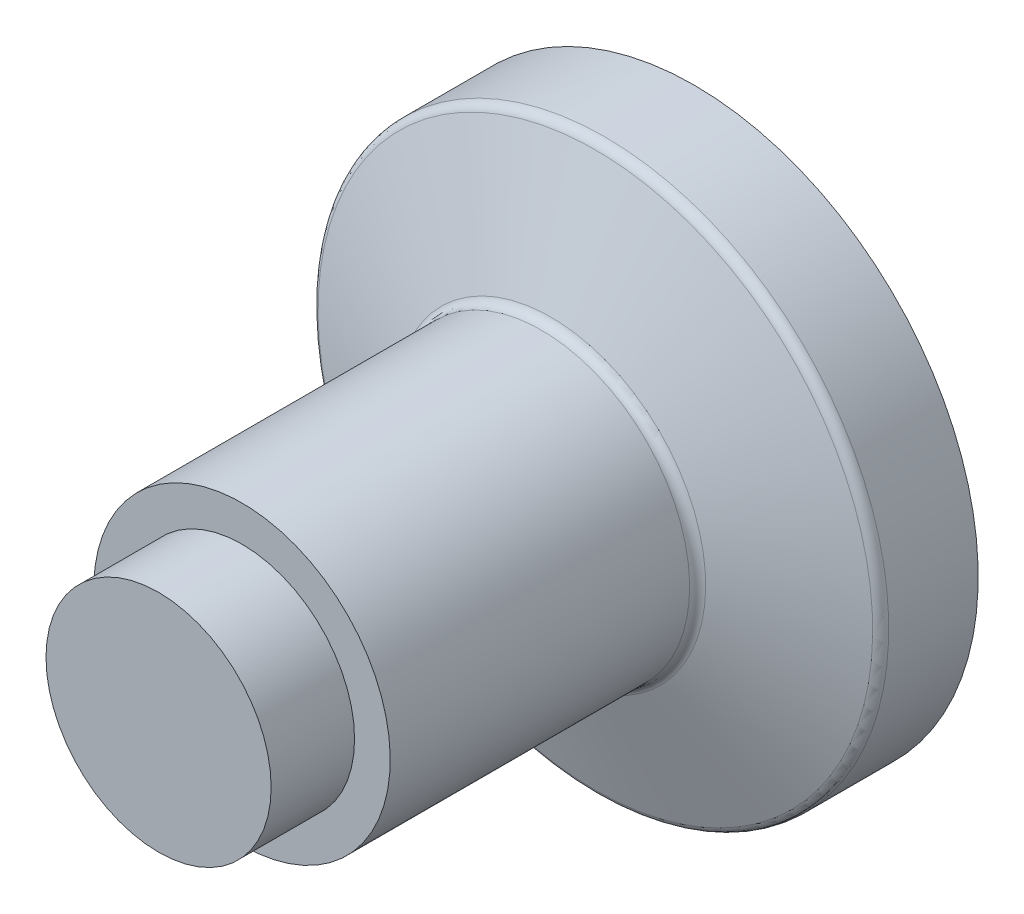
SolidWorks part; units mm, degrees
ref_plane "Front Plane" through (0, 0, 0) normal (0, 0, 1) x (1, 0, 0)
ref_plane "Top Plane" through (0, 0, 0) normal (0, 1, 0) x (1, 0, 0)
ref_plane "Right Plane" through (0, 0, 0) normal (1, 0, 0) x (0, 0, -1)
sketch "Sketch1" plane through (0, 0, 0) normal (1, 0, 0) x (0, 0, -1)
  line L0 (0, 0) -> (0, 11.2)
  line L1 (0, 55) -> (0, -55) construction
  line L2 (8.3, 14.75) -> (38.0862, 14.75)
  line L3 (39.0259, 15.408) -> (43.4605, 27.592)
  line L4 (44.4002, 28.25) -> (53.3, 28.25)
  line L5 (0, 0) -> (60.5, 0)
  line L6 (55, 0) -> (-55, 0) construction
  line L7 (53.3, 28.25) -> (53.3, 24.25)
  line L8 (8.3, 14.75) -> (8.3, 11.2)
  line L9 (8.3, 11.2) -> (0, 11.2)
  line L10 (0, 11.2) -> (0, 2.7718)
  line L11 (0, 11.2) -> (0, 14.75) construction
  line L12 (0, 14.75) -> (8.3, 14.75) construction
  arc A0 (53.3, 24.25) -> (60.5, 0) centre (16.0623, 0) cw
  arc A1 (44.4002, 28.25) -> (43.4605, 27.592) centre (44.4002, 27.25) ccw
  arc A2 (39.0259, 15.408) -> (38.0862, 14.75) centre (38.0862, 15.75) cw
  point P17 (43.7, 28.25)
  point P20 (38.7864, 14.75)
  dimension "D8" = 1
  dimension "D2" = 28.25
  dimension "D3" = 14.75
  dimension "D5" = 9.6
  dimension "D6" = 70
  dimension "D7" = 4
  dimension "D9" = 11.2
  dimension "D10" = 8.3
  dimension "D11" = 52.2
  dimension "D4" = 45
revolve "Revolve1" add sketch "Sketch1" angle 360 about L5
equation "\"D3@Sketch1\"=29.5/2"
equation "\"D2@Sketch1\"=56.5/2"
equation "\"D9@Sketch1\"=22.4/2"
